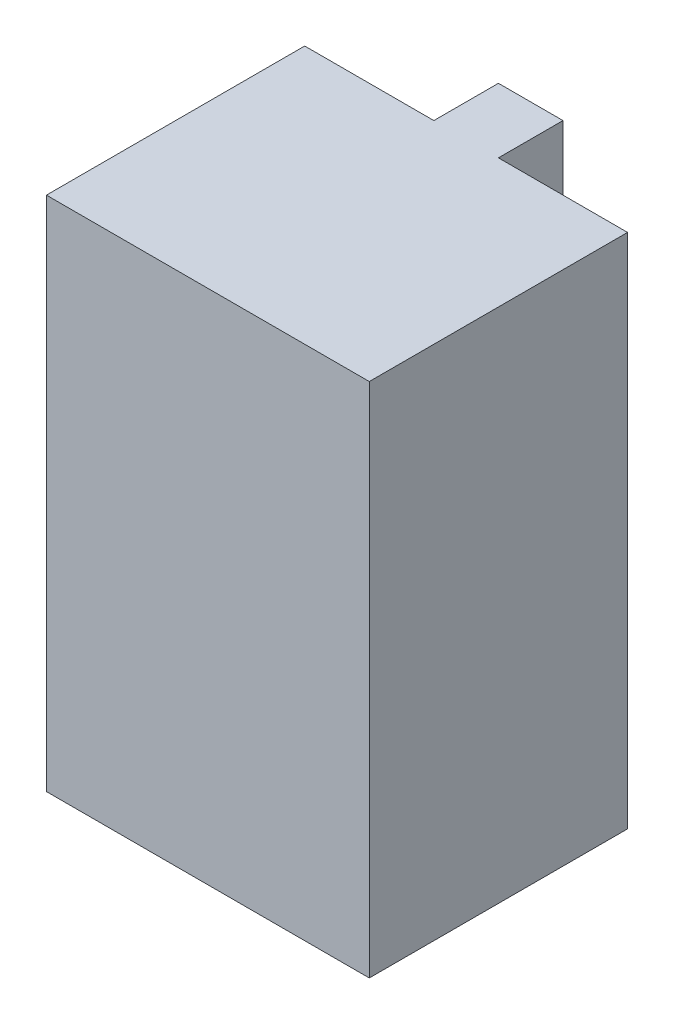
SolidWorks part; units mm, degrees
ref_plane "Plan de face" through (0, 0, 0) normal (0, 0, 1) x (1, 0, 0)
ref_plane "Plan de dessus" through (0, 0, 0) normal (0, 1, 0) x (1, 0, 0)
ref_plane "Plan de droite" through (0, 0, 0) normal (1, 0, 0) x (0, 0, -1)
other "Centre de masse"
sketch "Esquisse1" plane through (0, 0, 0) normal (0, 1, 0) x (1, 0, 0)
  line L0 (0, 40) -> (20, 40)
  line L1 (0, 0) -> (50, 0)
  line L2 (0, 0) -> (0, 40)
  line L4 (50, 0) -> (50, 40)
  line L5 (20, 40) -> (20, 50)
  line L6 (20, 50) -> (30, 50)
  line L7 (30, 50) -> (30, 40)
  line L8 (30, 40) -> (50, 40)
  dimension "D1" = 50
  dimension "D2" = 40
  dimension "D3" = 10
  dimension "D4" = 20
extrude "Boss.-Extru.1" add sketch "Esquisse1" along normal blind 80
other "Point de référence du centre de masse1"
ref_plane "PlanCDG" through (0, 40, 0) normal (0, 1, 0) x (1, 0, 0)
sketch "Esquisse4" plane through (0, 40, 0) normal (0, 1, 0) x (1, 0, 0)
  point P0 (25, 21.2)
  point P4 (7.4625, 10.993)
equation "\"CtrX\"= \"SW-Centre de gravitéX\""
equation "\"D1@PlanCDG\"=\"CentreY\""
equation "\"D2@Esquisse4\"=\"CentreZ\""
equation "\"D1@Esquisse4\"=\"CentreX\""
equation "\"CtrY\"= \"SW-Centre de gravitéY\""
equation "\"CtrZ\"= abs ( \"SW-Centre de gravitéZ\" )"
